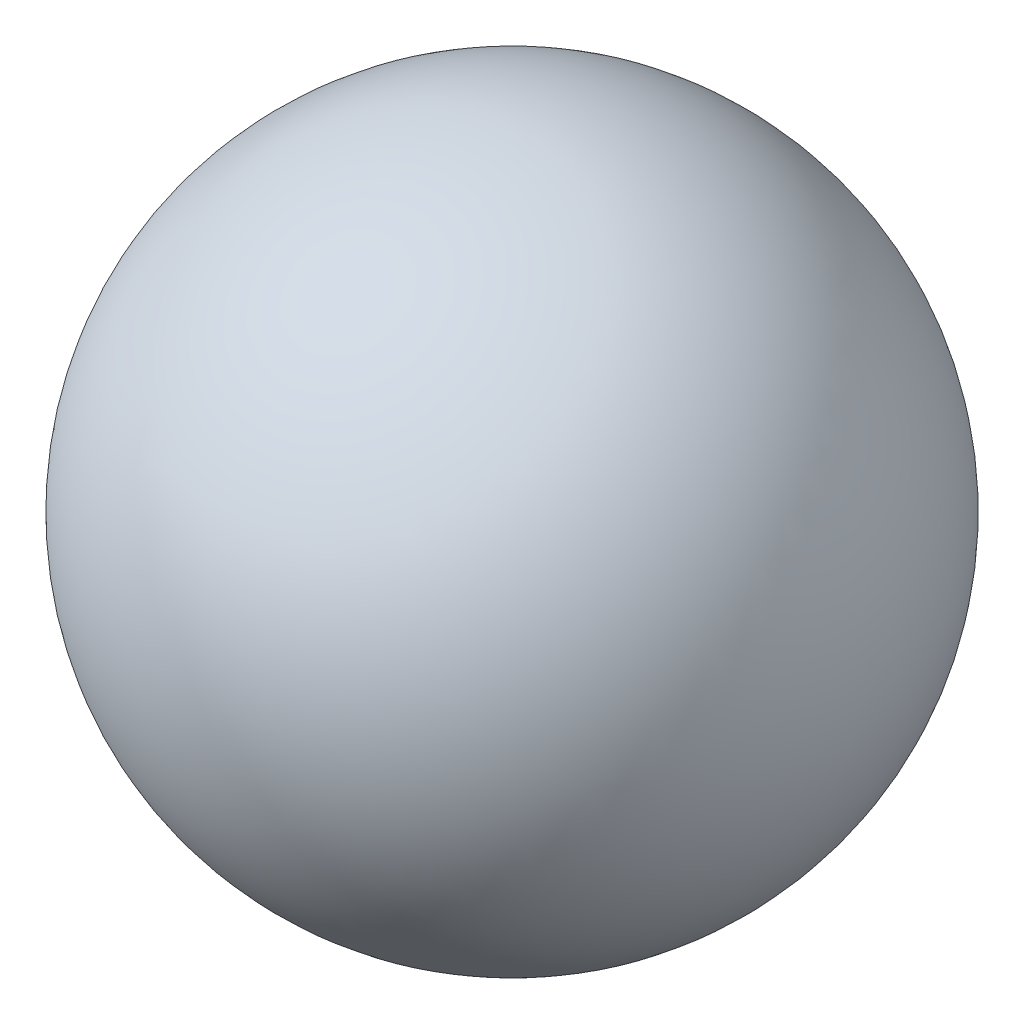
SolidWorks part; units mm, degrees
material "1.4000 (X6Cr13)"
ref_plane "Přední rovina" through (0, 0, 0) normal (0, 0, 1) x (1, 0, 0)
ref_plane "Horní rovina" through (0, 0, 0) normal (0, 1, 0) x (1, 0, 0)
ref_plane "Pravá rovina" through (0, 0, 0) normal (1, 0, 0) x (0, 0, -1)
sketch "Skica1" plane through (0, 0, 0) normal (0, 0, 1) x (1, 0, 0)
  line L0 (0, 2.5) -> (0, -2.5) construction
  line L1 (0, 2.5) -> (0, -2.5)
  arc A0 (0, 2.5) -> (0, -2.5) centre (0, 0) ccw
  dimension "D1" = 5
revolve "Rotovat3" add sketch "Skica1" angle 360 about L0
